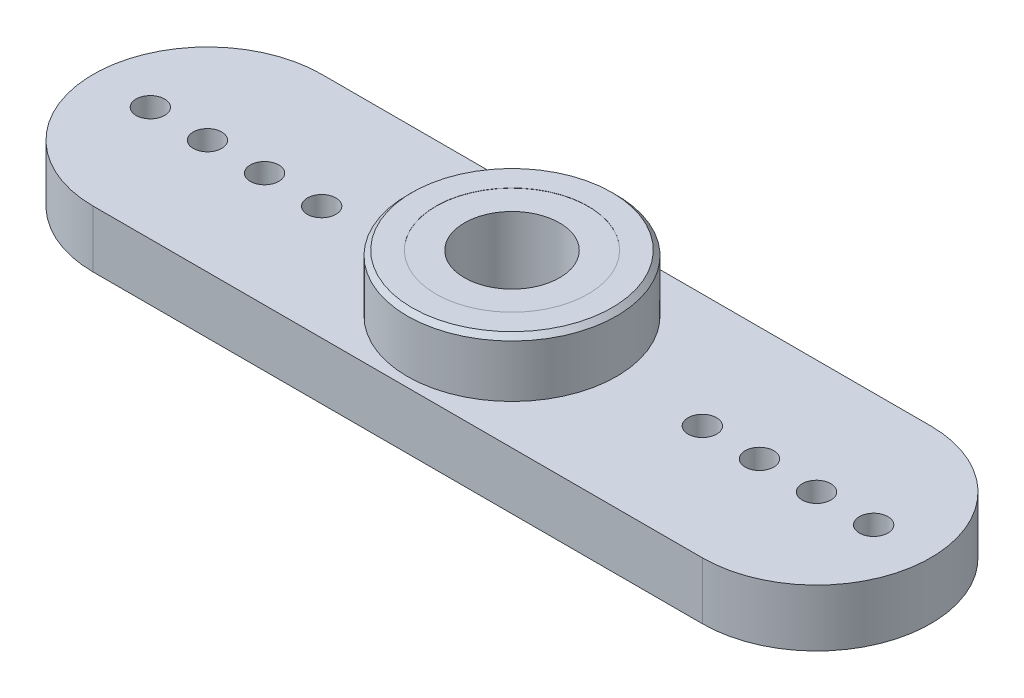
SolidWorks part; units mm, degrees
ref_plane "Front Plane" through (0, 0, 0) normal (0, 0, 1) x (1, 0, 0)
ref_plane "Top Plane" through (0, 0, 0) normal (0, 1, 0) x (1, 0, 0)
ref_plane "Right Plane" through (0, 0, 0) normal (1, 0, 0) x (0, 0, -1)
sketch "Sketch1" plane through (0, 0, 0) normal (0, 1, 0) x (1, 0, 0)
  line L0 (-16, 0) -> (16, 0) construction
  line L1 (-16, 6) -> (16, 6)
  line L2 (-16, -6) -> (16, -6)
  line L3 (0, 6) -> (0, -6) construction
  arc A0 (-16, 6) -> (-16, -6) centre (-16, 0) ccw
  arc A1 (16, -6) -> (16, 6) centre (16, 0) ccw
  circle A2 centre (10, 0) radius 0.75
  circle A3 centre (13, 0) radius 0.75
  circle A4 centre (16, 0) radius 0.75
  circle A5 centre (19, 0) radius 0.75
  circle A6 centre (-19, 0) radius 0.75
  circle A7 centre (-16, 0) radius 0.75
  circle A8 centre (-13, 0) radius 0.75
  circle A9 centre (-10, 0) radius 0.75
  circle A10 centre (0, 0) radius 1.5
  point P3 (0, 0)
  dimension "D2" = 32
  dimension "D3" = 1.5
  dimension "D4" = 3
  dimension "D5" = 3
  dimension "D6" = 3
  dimension "D7" = 38
  dimension "D8" = 3
  dimension "D1" = 12
extrude "Boss-Extrude1" add sketch "Sketch1" along normal blind 3
sketch "Sketch2" plane through (0, 0, 0) normal (0, -1, 0) x (-1, 0, 0)
  circle A0 centre (0, 0) radius 3.5
  dimension "D1" = 7
extrude "Cut-Extrude1" cut sketch "Sketch2" against normal blind 1.5
sketch "Sketch3" plane through (0, 3, 0) normal (0, 1, 0) x (1, 0, 0)
  circle A0 centre (0, 0) radius 4
  dimension "D1" = 8
extrude "Boss-Extrude2" add sketch "Sketch3" along normal blind 2.99
sketch "Sketch4" plane through (0, 5.99, 0) normal (0, 1, 0) x (1, 0, 0)
  circle A0 centre (0, 0) radius 2.5
  dimension "D1" = 5
extrude "Cut-Extrude2" cut sketch "Sketch4" against normal blind 4
sketch "Sketch5" plane through (0, 3, 0) normal (0, 1, 0) x (1, 0, 0)
  circle A0 centre (0, 0) radius 4
  circle A1 centre (0, 0) radius 5.5
  circle A2 centre (0, 0) radius 4 construction
  dimension "D1" = 11
extrude "Boss-Extrude3" add sketch "Sketch5" along normal blind 3
chamfer "Chamfer1" distance 0.25 angle 45 1 edges at (0, 6, 5.5)
